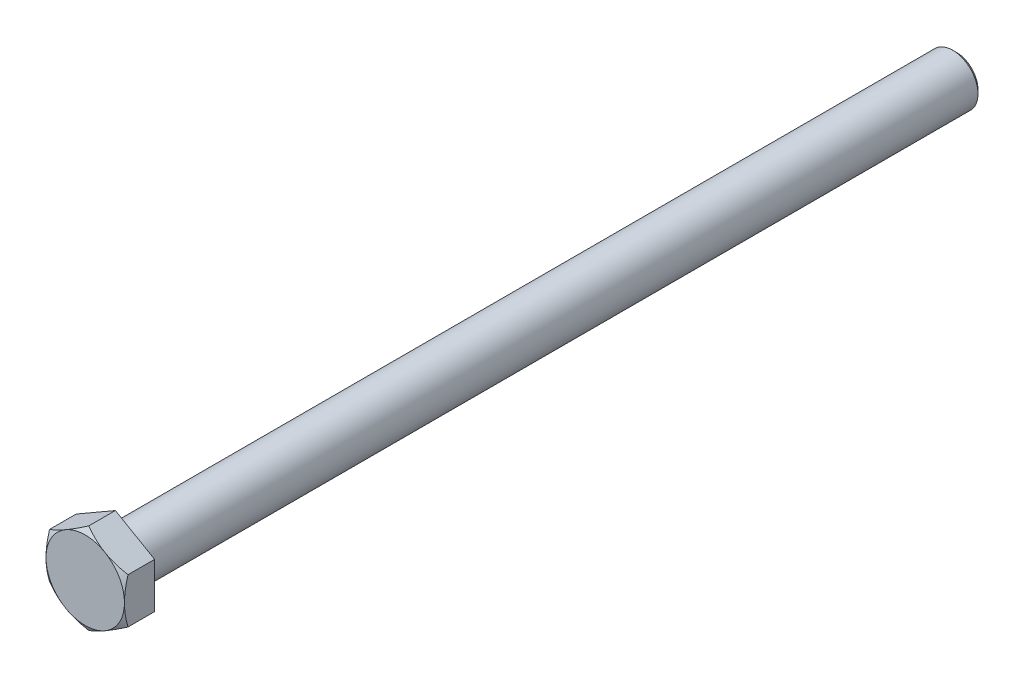
SolidWorks part; units mm, degrees
ref_plane "Front Plane" through (0, 0, 0) normal (0, 0, 1) x (1, 0, 0)
ref_plane "Top Plane" through (0, 0, 0) normal (0, 1, 0) x (1, 0, 0)
ref_plane "Right Plane" through (0, 0, 0) normal (1, 0, 0) x (0, 0, -1)
sketch "Sketch1" plane through (0, 0, 0) normal (0, 0, 1) x (1, 0, 0)
  line L0 (0, 0) -> (0, 10.7791) construction
  line L2 (0, 10.7791) -> (-9.335, 5.3896)
  line L3 (-9.335, 5.3896) -> (-9.335, -5.3896)
  line L4 (-9.335, -5.3896) -> (0, -10.7791)
  line L5 (0, -10.7791) -> (9.335, -5.3896)
  line L6 (9.335, -5.3896) -> (9.335, 5.3896)
  line L7 (9.335, 5.3896) -> (0, 10.7791)
  circle A0 centre (0, 0) radius 9.335 construction
  dimension "HEX" = 18.67
extrude "Boss-Extrude1" add sketch "Sketch1" along normal blind 7.32
sketch "Sketch2" plane through (0, 0, 0) normal (1, 0, 0) x (0, 0, -1)
  line L0 (0, 0) -> (200, 0) construction
  line L1 (0, 0) -> (0, 6.6)
  line L4 (199.1, 6) -> (200, 5.1)
  line L7 (200, 5.1) -> (200, 0)
  line L8 (200, 0) -> (0, 0)
  line L9 (199.1, 6) -> (0.6, 6)
  arc A3 (0.6, 6) -> (0, 6.6) centre (0.6, 6.6) cw
  dimension "D1" = 0.6
  dimension "LENGTH" = 200
  dimension "WIDTH2" = 10.2
  dimension "WIDTH1" = 12
  dimension "D5" = 45
revolve "Revolve1" add sketch "Sketch2" angle 360 about L0
cosmetic thread "Cosmetic Thread1" parameters "D1"=110, "D2"=12
sketch "Sketch3" plane through (0, 0, 0) normal (1, 0, 0) x (0, 0, -1)
  line L0 (-12.2049, 0) -> (129.7862, 0) construction
  line L1 (-7.32, 10.7791) -> (-6.4862, 10.7791)
  line L2 (-0.15, 10.7791) -> (-0.15, 8.7866)
  line L3 (-6.4862, 10.7791) -> (-7.32, 9.335)
  line L4 (-0.15, 8.7866) -> (0, 8.7)
  line L5 (-7.32, 9.335) -> (-7.32, 10.7791)
  line L6 (0, -5.3896) -> (0, 5.3896) construction
  line L7 (-7.32, 10.7791) -> (0, 10.7791) construction
  line L8 (-7.32, 5.3896) -> (-7.32, 10.7791) construction
  line L10 (0, 8.7) -> (0, 10.7791)
  line L11 (0, 10.7791) -> (-0.15, 10.7791)
  dimension "D1" = 30
  dimension "SAME AS HEX" = 18.67
  dimension "D3" = 30
  dimension "C" = 0.15
  dimension "DW" = 17.4
revolve "Cut-Revolve1" cut sketch "Sketch3" angle 360 about L0
